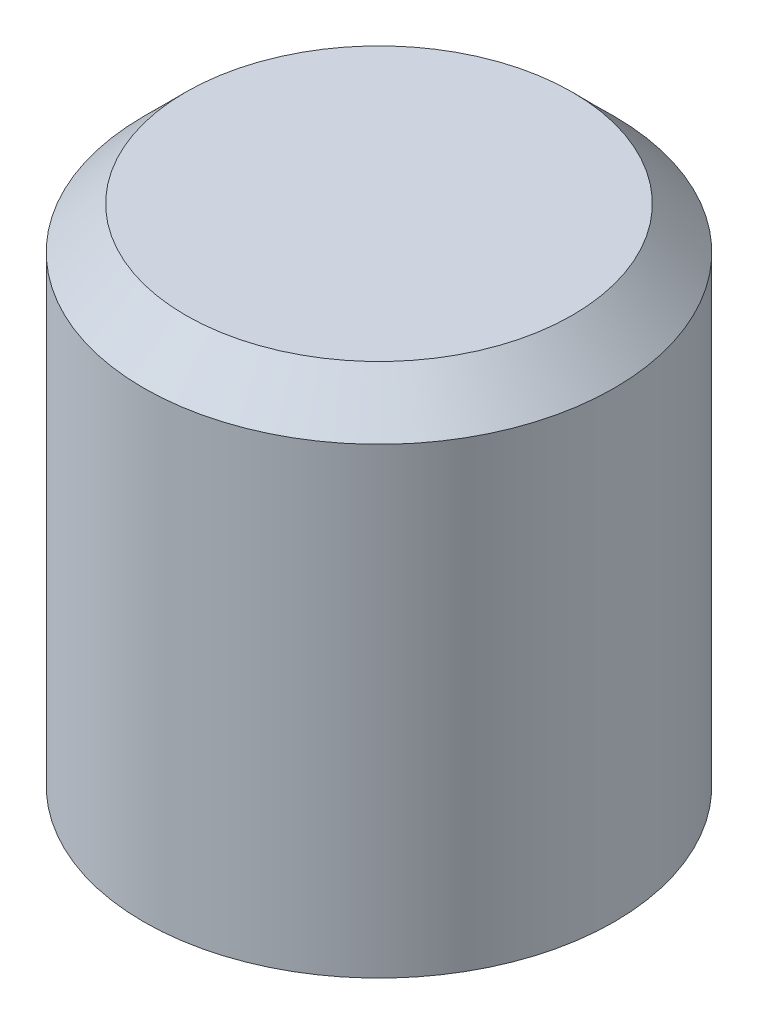
SolidWorks part; units mm, degrees
ref_plane "Front Plane" through (0, 0, 0) normal (0, 0, 1) x (1, 0, 0)
ref_plane "Top Plane" through (0, 0, 0) normal (0, 1, 0) x (1, 0, 0)
ref_plane "Right Plane" through (0, 0, 0) normal (1, 0, 0) x (0, 0, -1)
sketch "Sketch1" plane through (0, 0, 0) normal (0, 1, 0) x (1, 0, 0)
  circle A0 centre (0, 0) radius 1.4
extrude "Boss-Extrude1" add sketch "Sketch1" along normal blind 3
chamfer "Chamfer1" distance 0.25 angle 45 1 edges at (0, 3, 1.4)
